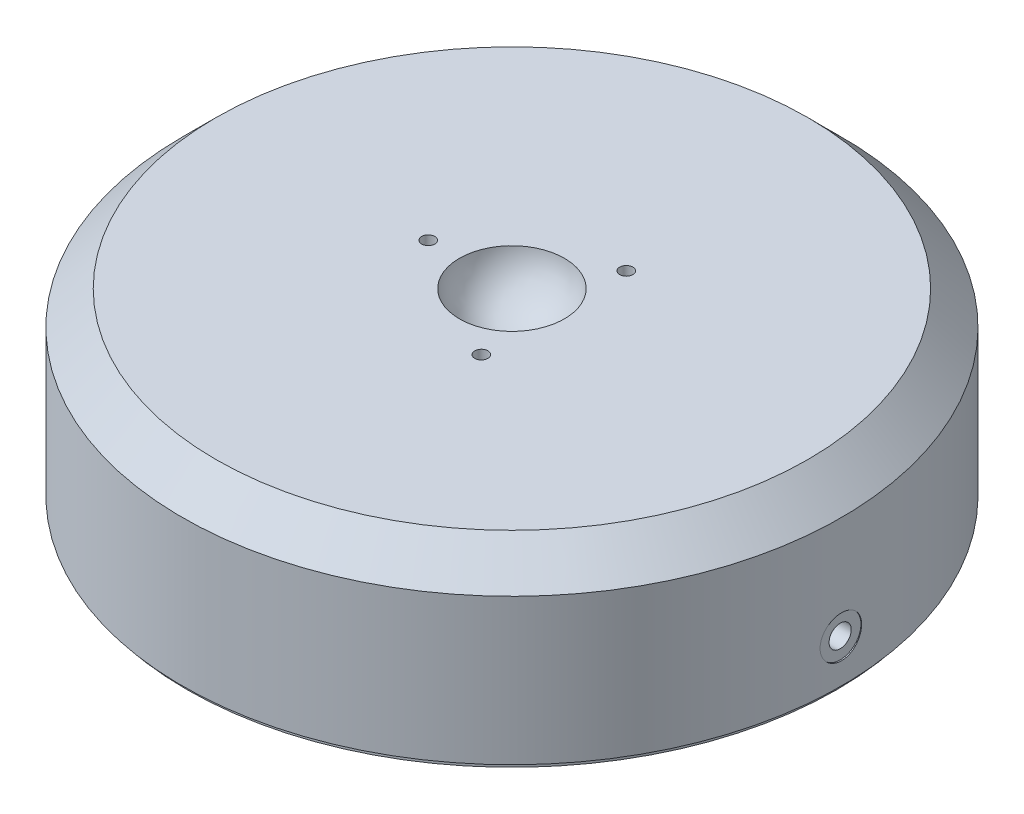
SolidWorks part; units mm, degrees
material "6061 Alloy"
ref_plane "Front Plane" through (0, 0, 0) normal (0, 0, 1) x (1, 0, 0)
ref_plane "Top Plane" through (0, 0, 0) normal (0, 1, 0) x (1, 0, 0)
ref_plane "Right Plane" through (0, 0, 0) normal (1, 0, 0) x (0, 0, -1)
sketch "Sketch1" plane through (0, 0, 0) normal (0, 0, 1) x (1, 0, 0)
  line L0 (0, 0) -> (62.4967, 0)
  line L1 (62.4967, 0) -> (62.4967, 27.6606)
  line L2 (62.4967, 27.6606) -> (56.1467, 34.0106)
  line L3 (56.1467, 34.0106) -> (9.9559, 34.0106)
  line L4 (0, 23.9776) -> (0, 0) construction
  line L5 (0, 24.6126) -> (2.3876, 24.6126)
  line L6 (2.3876, 24.6126) -> (2.3876, 25.308)
  line L7 (0, 24.6126) -> (0, 0)
  arc A0 (2.3876, 25.308) -> (9.9559, 34.0106) centre (0, 35.0266) ccw
  dimension "D1" = 10.0076
  dimension "D2" = 9.398
  dimension "D3" = 4.7752
  dimension "D4" = 1.016
  dimension "D5" = 34.0106
  dimension "D6" = 62.4967
  dimension "D7" = 6.35
  dimension "D8" = 45
revolve "Revolve1" add sketch "Sketch1" angle 360 about L4
sketch "Sketch2" plane through (0, 0, 0) normal (0, -1, 0) x (1, 0, 0)
  circle A0 centre (0, 0) radius 61.6585
  dimension "D1" = 123.317
hole_wizard "M5x0.8 Tapped Hole1" positions "3DSketch1" profile "Sketch4" tap size "M5x0.8" standard "Ansi Metric"
sketch3d "3DSketch1"
  point P0 (62.4967, 8.0772, 0)
  dimension "D1" = 25.9334
sketch "Sketch4" plane through (62.4967, 8.0772, 0) normal (0, 1, 0) x (0, 0, -1)
  line L0 (0, 0) -> (0, 48.2518)
  line L1 (0, 48.2518) -> (2.1, 46.99)
  line L2 (2.1, 46.99) -> (2.1, 0)
  line L5 (2.1, 0) -> (0, 0)
  line L10 (0, 48.2518) -> (-2.1, 46.99) construction
  line L11 (0, -6.35) -> (0, 107.95) construction
  dimension "Tap Drill Dia." = 4.2
  dimension "Tap Drill Depth" = 46.99
  dimension "Drill Angle" = 118
cosmetic thread "Hole Thread2" parameters "D1"=7.62, "D2"=5
hole_wizard "M3x0.5 Tapped Hole1" positions "Sketch6" profile "Sketch5" tap size "M3x0.5" standard "Ansi Metric"
sketch "Sketch6" plane through (0, 34.0106, 0) normal (0, 1, 0) x (-1, 0, 0)
  line L0 (18.7058, 0) -> (-18.7058, 0) construction
  point P0 (15.875, 0)
  dimension "D1" = 15.875
sketch "Sketch5" plane through (-15.875, 34.0106, 0) normal (1, 0, 0) x (0, 0, 1)
  line L0 (0, 0) -> (0, 10.4031)
  line L1 (0, 10.4031) -> (1.25, 9.652)
  line L2 (1.25, 9.652) -> (1.25, 0)
  line L5 (1.25, 0) -> (0, 0)
  line L10 (0, 10.4031) -> (-1.25, 9.652) construction
  line L11 (0, -6.35) -> (0, 107.95) construction
  dimension "Tap Drill Dia." = 2.5
  dimension "Tap Drill Depth" = 9.652
  dimension "Drill Angle" = 118
cosmetic thread "Hole Thread1" parameters "D1"=6.1, "D2"=3
pattern_circular "CirPattern1" count 3 every 120 about axis through (0, 0, 0) along (0, 1, 0) of "M3x0.5 Tapped Hole1"
hole_wizard "CBORE for #00 Binding Head Machine Screw1" positions "3DSketch2" profile "Sketch7" counterbore size "#00" standard "Ansi Inch"
sketch3d "3DSketch2"
  point P3 (62.4967, 8.0772, 0)
sketch "Sketch7" plane through (62.4967, 8.0772, 0) normal (0, 1, 0) x (0, 0, -1)
  line L0 (0, 0) -> (0, 6.7697)
  line L1 (0, 6.7697) -> (0.6985, 6.35)
  line L2 (0.6985, 6.35) -> (0.6985, 0.254)
  line L3 (0.6985, 0.254) -> (3.937, 0.254)
  line L4 (3.937, 0.254) -> (3.937, 0)
  line L5 (3.937, 0) -> (0, 0)
  line L10 (0, 6.7697) -> (-0.6985, 6.35) construction
  line L11 (0, -6.35) -> (0, 107.95) construction
  dimension "Hole Dia." = 1.397
  dimension "Hole Depth" = 6.35
  dimension "C'Bore Dia." = 7.874
  dimension "C'Bore Depth" = 0.254
  dimension "Drill Angle" = 118
extrude "Extrude1" add sketch "Sketch2" along normal blind 1.016
